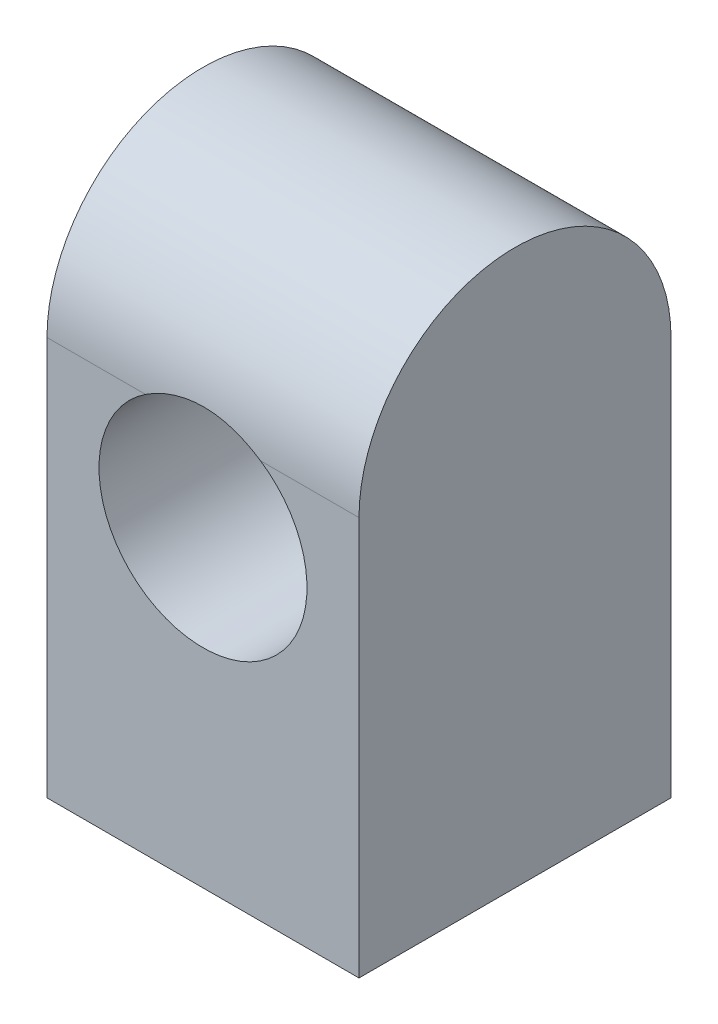
SolidWorks part; units mm, degrees
ref_plane "Front Plane" through (0, 0, 0) normal (0, 0, 1) x (1, 0, 0)
ref_plane "Top Plane" through (0, 0, 0) normal (0, 1, 0) x (1, 0, 0)
ref_plane "Right Plane" through (0, 0, 0) normal (1, 0, 0) x (0, 0, -1)
sketch "Sketch1" plane through (0, 0, 0) normal (1, 0, 0) x (0, 0, -1)
  line L2 (-10, 17.1399) -> (-10, -5.8601)
  line L3 (-10, -5.8601) -> (8, -5.8601)
  line L4 (8, 17.1399) -> (8, -5.8601)
  arc A0 (-10, 17.1399) -> (8, 17.1399) centre (-1, 17.1399) cw
  point P0 (0, 0)
  dimension "D1" = 9
  dimension "D3" = 18
  dimension "D2" = 23
extrude "Boss-Extrude1" add sketch "Sketch1" along normal blind 18
sketch "Sketch2" plane through (0, 0, 10) normal (0, 0, 1) x (1, 0, 0)
  line L0 (18, -5.8601) -> (0, -5.8601) construction
  line L2 (0, 17.1399) -> (0, -5.8601) construction
  circle A0 centre (9, 12.1399) radius 6
  dimension "D1" = 12
  dimension "D2" = 18
  dimension "D3" = 9
extrude "Cut-Extrude1" cut sketch "Sketch2" against normal through all
sketch "Sketch3" plane through (0, -5.8601, 0) normal (0, -1, 0) x (1, 0, 0)
  line L0 (9, 10) -> (9, 5.6011) construction
  line L1 (5, -2.3989) -> (13, -2.3989)
  line L2 (5, -2.3989) -> (5, 5.6011)
  line L3 (5, 5.6011) -> (13, 5.6011)
  line L4 (13, -2.3989) -> (13, 5.6011)
  line L5 (5, -2.3989) -> (13, 5.6011) construction
  line L6 (5, 5.6011) -> (13, -2.3989) construction
  line L7 (18, 10) -> (0, 10) construction
  point P0 (9, 1.6011)
  dimension "D1" = 8
hole_wizard "M4x0.7 Tapped Hole2" positions "Sketch6" profile "Sketch7" tap size "M4x0.7" standard "BSI"
sketch "Sketch6" plane through (0, -5.8601, 0) normal (0, -1, 0) x (-1, 0, 0)
  point P0 (-5, -5.6011)
  point P3 (-5, 2.3989)
  point P6 (-13, 2.3989)
  point P9 (-13, -5.6011)
sketch "Sketch7" plane through (5, -5.8601, 5.6011) normal (1, 0, 0) x (0, 0, -1)
  line L0 (0, 0) -> (0, 11.0914)
  line L1 (0, 11.0914) -> (1.65, 10.1)
  line L2 (1.65, 10.1) -> (1.65, 0.375)
  line L3 (1.65, 0.375) -> (2.025, 0)
  line L5 (2.025, 0) -> (0, 0)
  line L6 (-1.65, 0.375) -> (-2.025, 0) construction
  line L10 (0, 11.0914) -> (-1.65, 10.1) construction
  line L11 (0, -6.35) -> (0, 107.95) construction
  dimension "Tap Drill Dia." = 3.3
  dimension "Tap Drill Depth" = 10.1
  dimension "Near C'Sink Dia." = 4.05
  dimension "Near C'Sink Angle" = 90
  dimension "Drill Angle" = 118
cosmetic thread "Hole Thread2" parameters "D1"=8, "D2"=4
cosmetic thread "Hole Thread3" parameters "D1"=8, "D2"=4
cosmetic thread "Hole Thread4" parameters "D1"=8, "D2"=4
cosmetic thread "Hole Thread5" parameters "D1"=8, "D2"=4
